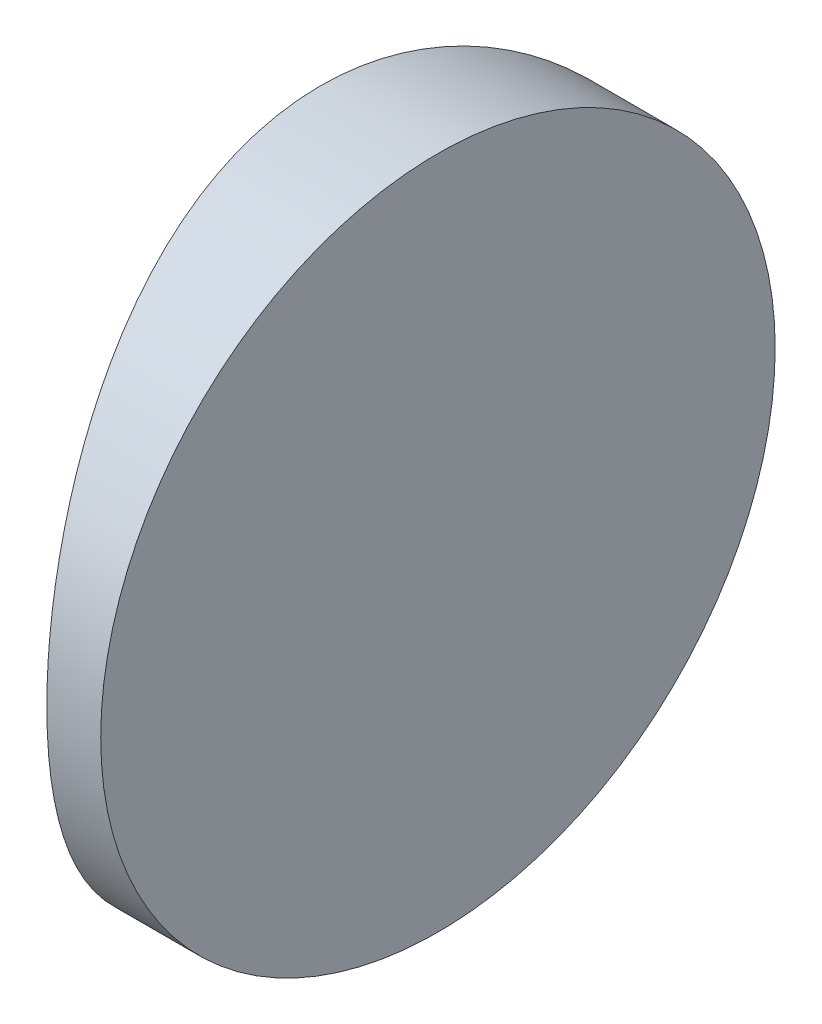
SolidWorks part; units mm, degrees
ref_plane "前视基准面" through (0, 0, 0) normal (0, 0, 1) x (1, 0, 0)
ref_plane "上视基准面" through (0, 0, 0) normal (0, 1, 0) x (1, 0, 0)
ref_plane "右视基准面" through (0, 0, 0) normal (1, 0, 0) x (0, 0, -1)
sketch "草图1" plane through (0, 0, 0) normal (0, 1, 0) x (1, 0, 0)
  line L0 (10.7432, 0) -> (-55.502, 0) construction
  line L1 (-27.6826, 12.5) -> (-25.6848, 12.5)
  line L2 (-27.6826, -12.5) -> (-25.6848, -12.5)
  line L3 (-25.6848, 12.5) -> (-25.6848, -12.5)
  arc A0 (-27.6826, 12.5) -> (-27.6826, -12.5) centre (4.3552, 0) ccw
  point P19 (-30.0348, 0)
  point P20 (-25.6848, 0)
  dimension "D2" = 12.5
  dimension "D3" = 34.39
  dimension "D4" = 4.35
  dimension "D1" = 12.5
extrude "凸台-拉伸1" add sketch "草图1" along normal blind 25 contours A0 L2 L3 L1
sketch "草图2" plane through (-25.6848, 0, 0) normal (1, 0, 0) x (0, 0, -1)
  line L0 (12.5, 0) -> (-12.5, 0) construction
  line L7 (-12.5, 0) -> (12.5, 0)
  line L8 (12.5, 0) -> (12.5, 25)
  line L9 (12.5, 25) -> (-12.5, 25)
  line L10 (-12.5, 25) -> (-12.5, 0)
  line L11 (-12.5, 0) -> (12.5, 0)
  line L12 (12.5, 0) -> (12.5, 25)
  line L13 (12.5, 25) -> (-12.5, 25)
  line L14 (-12.5, 25) -> (-12.5, 0)
  circle A0 centre (0, 12.5) radius 12.5
  line M1 (-12.5, 0) -> (12.5, 0)
  line M2 (12.5, 0) -> (12.5, 25)
  line M3 (12.5, 25) -> (-12.5, 25)
  line M4 (-12.5, 25) -> (-12.5, 0)
  dimension "D1" = 25
  dimension "D4" = 12.5
  dimension "D2" = 12.5
  dimension "D3" = 0
extrude "切除-拉伸8" cut sketch "草图2" against normal blind 12.7 contours A0 L13 M4 | A0 L12 M3 | A0 L11 M2 | A0 L14 M1
